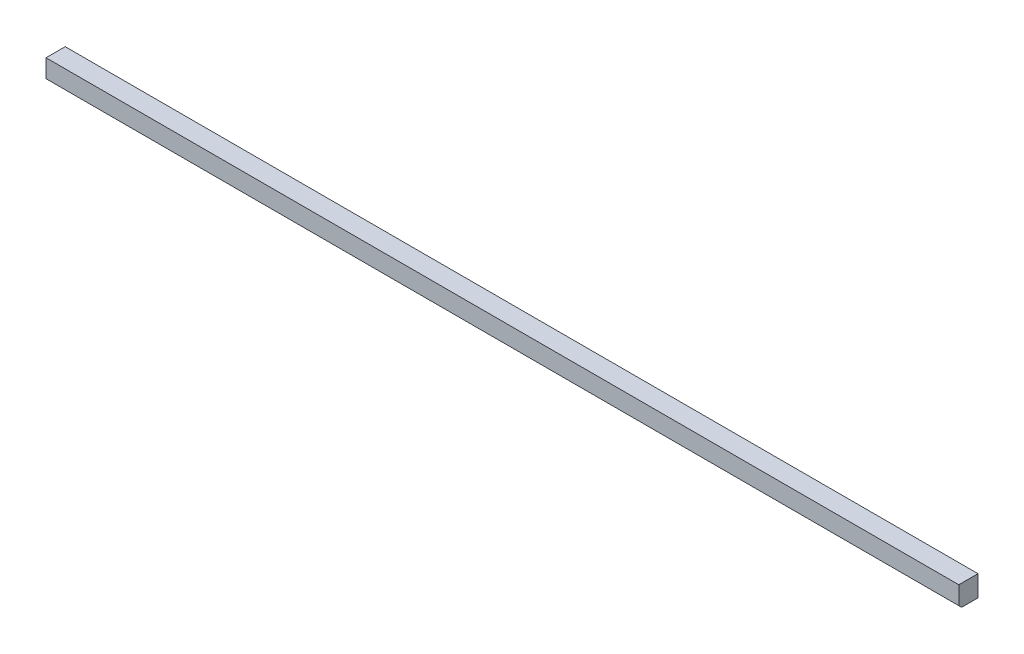
SolidWorks part; units mm, degrees
material "Oak"
ref_plane "Front Plane" through (0, 0, 0) normal (0, 0, 1) x (1, 0, 0)
ref_plane "Top Plane" through (0, 0, 0) normal (0, 1, 0) x (1, 0, 0)
ref_plane "Right Plane" through (0, 0, 0) normal (1, 0, 0) x (0, 0, -1)
sketch "Sketch1" plane through (0, 0, 0) normal (0, 1, 0) x (1, 0, 0)
  line L1 (0, 0) -> (830.2625, 0)
  line L2 (0, 0) -> (0, 17.4625)
  line L3 (0, 17.4625) -> (830.2625, 17.4625)
  line L4 (830.2625, 0) -> (830.2625, 17.4625)
  dimension "D1" = 17.4625
  dimension "D2" = 830.2625
extrude "Boss-Extrude1" add sketch "Sketch1" along normal blind 19.05
chamfer "Chamfer1" distance 2.54 angle 45 1 edges at (415.1313, 0, 0)
